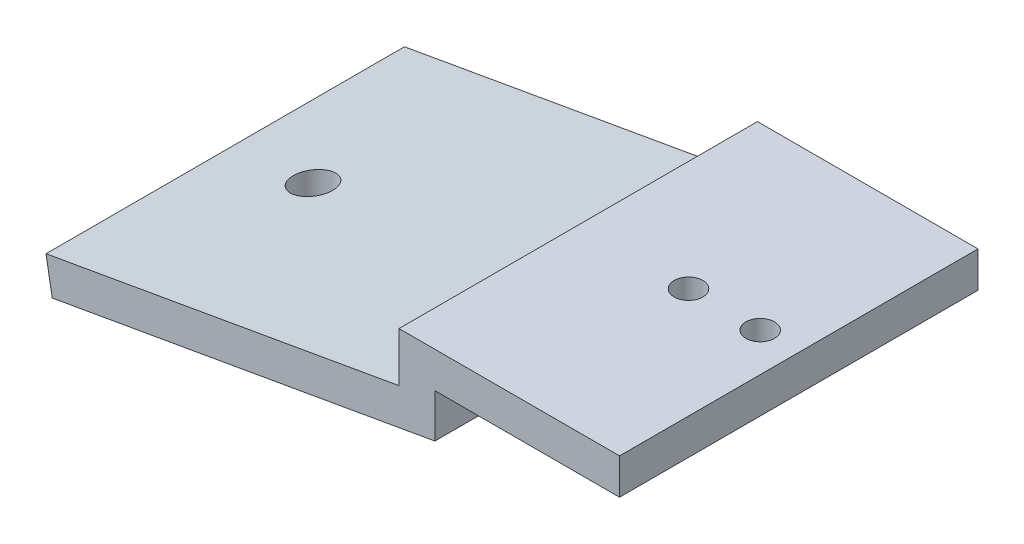
SolidWorks part; units mm, degrees
ref_plane "Front Plane" through (0, 0, 0) normal (0, 0, 1) x (1, 0, 0)
ref_plane "Top Plane" through (0, 0, 0) normal (0, 1, 0) x (1, 0, 0)
ref_plane "Right Plane" through (0, 0, 0) normal (1, 0, 0) x (0, 0, -1)
sketch "Sketch1" plane through (0, 0, 0) normal (0, 0, 1) x (1, 0, 0)
  line L0 (0, 0) -> (-28.2596, 0) construction
  line L1 (-28.2596, 0) -> (-28.2596, -6.4956)
  line L2 (-28.2596, -6.4956) -> (-79.5659, -15.5423) construction
  line L3 (0, 2.5) -> (-30.7596, 2.5)
  line L4 (-30.7596, 2.5) -> (-30.7596, -4.3979)
  line L5 (-30.7596, -4.3979) -> (-80, -13.0803)
  line L6 (0, -2.5) -> (-25.7596, -2.5)
  line L7 (-25.7596, -2.5) -> (-25.7596, -8.5934)
  line L8 (-25.7596, -8.5934) -> (-79.1318, -18.0043)
  line L9 (-80, -13.0803) -> (-79.1318, -18.0043)
  line L10 (0, 2.5) -> (0, -2.5)
  dimension "D1" = 2.5
  dimension "D3" = 50
  dimension "D4" = 100
  dimension "D5" = 80
  dimension "D6" = 4.3979
  dimension "D2" = 2.5
extrude "Boss-Extrude1" add sketch "Sketch1" along normal blind 50
ref_plane "Plane1" through (0, 2.5, 0) normal (0, 1, 0) x (1, 0, 0)
sketch "Sketch2" plane through (0, 2.5, 0) normal (0, 1, 0) x (1, 0, 0)
  line L1 (-80, -50) -> (-80, 0) construction
  line L2 (0, 0) -> (-30.7596, 0) construction
  line L3 (0, -50) -> (0, 0) construction
  line L4 (-30.7596, -50) -> (-30.7596, 0) construction
  circle A0 centre (-67.7596, -25) radius 2.75
  circle A1 centre (-15.3798, -25) radius 2
  circle A2 centre (-5.3798, -25) radius 2
  point P4 (0, 0)
  point P9 (-80, -25)
  point P13 (-15.3798, 0)
  point P17 (0, -25)
  dimension "D1" = 5.5
  dimension "D2" = 4
  dimension "D3" = 4
  dimension "D4" = 10
  dimension "D5" = 37
extrude "Cut-Extrude1" cut sketch "Sketch2" against normal blind 50
